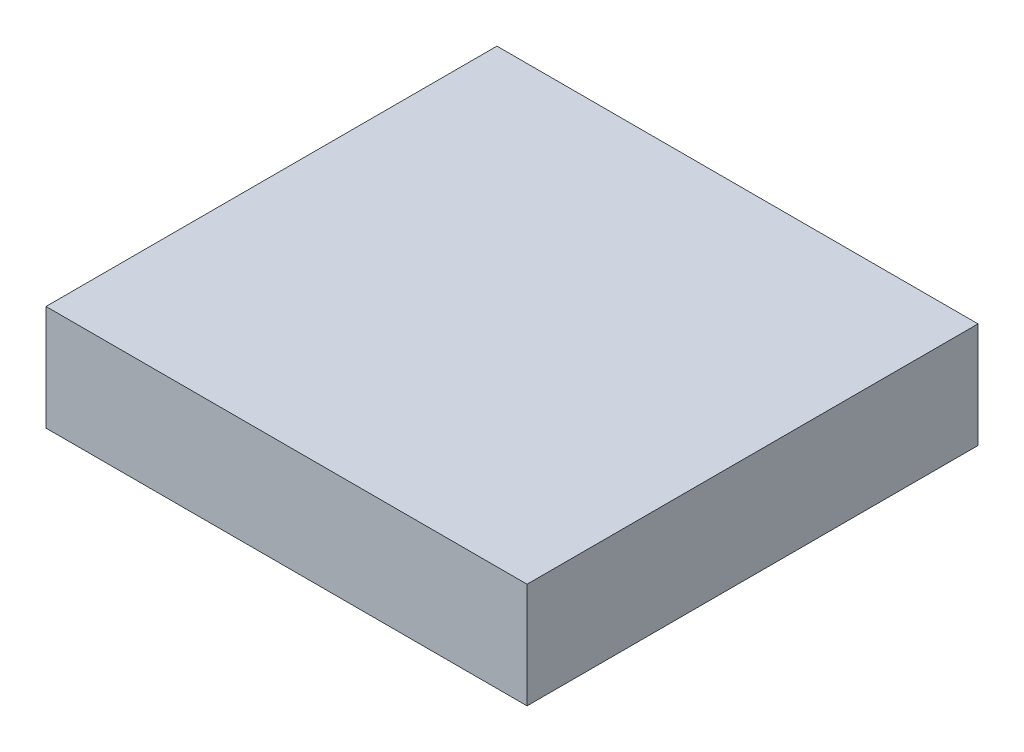
SolidWorks part; units mm, degrees
ref_plane "Front Plane" through (0, 0, 0) normal (0, 0, 1) x (1, 0, 0)
ref_plane "Top Plane" through (0, 0, 0) normal (0, 1, 0) x (1, 0, 0)
ref_plane "Right Plane" through (0, 0, 0) normal (1, 0, 0) x (0, 0, -1)
sketch "Sketch1" plane through (0, 0, 0) normal (0, 1, 0) x (1, 0, 0)
  line L1 (0, 0) -> (21.336, 0)
  line L2 (0, 0) -> (0, 20)
  line L3 (0, 20) -> (21.336, 20)
  line L4 (21.336, 0) -> (21.336, 20)
  dimension "D1" = 20
  dimension "D2" = 21.336
extrude "Boss-Extrude1" add sketch "Sketch1" along normal blind 4.6736
